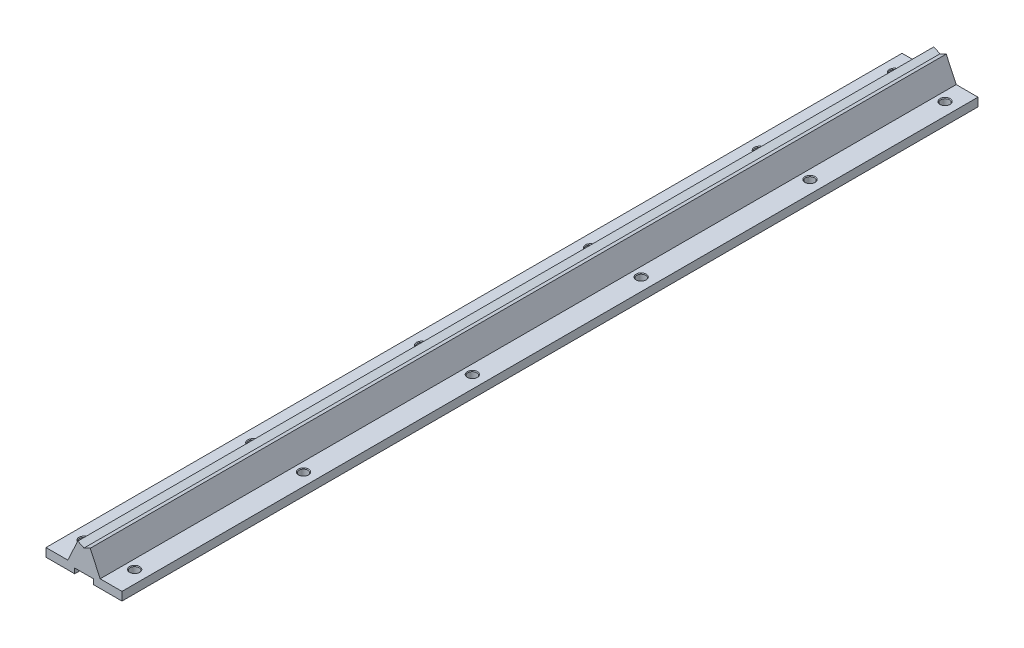
SolidWorks part; units mm, degrees
ref_plane "Front Plane" through (0, 0, 0) normal (0, 0, 1) x (1, 0, 0)
ref_plane "Top Plane" through (0, 0, 0) normal (0, 1, 0) x (1, 0, 0)
ref_plane "Right Plane" through (0, 0, 0) normal (1, 0, 0) x (0, 0, -1)
sketch "Sketch1" plane through (0, 0, 0) normal (0, 0, 1) x (1, 0, 0)
  line L0 (0, 0) -> (0, 30.5108) construction
  line L1 (0, 0) -> (-14.4586, 0) construction
  line L2 (5.5, 3) -> (-5.5, 3)
  line L3 (-5.5, 3) -> (-5.5, 0)
  line L4 (-5.5, 0) -> (-22.5, 0)
  line L5 (-22.5, 0) -> (-22.5, 5)
  line L6 (-22.5, 5) -> (-9.5977, 5)
  line L7 (-3.6756, 17.7) -> (3.6756, 17.7) construction
  line L8 (-3.6756, 17.7) -> (-9.5977, 5)
  line L9 (5.5, 3) -> (5.5, 0)
  line L10 (5.5, 0) -> (22.5, 0)
  line L11 (22.5, 0) -> (22.5, 5)
  line L12 (3.6756, 17.7) -> (9.5977, 5)
  line L13 (-3.6756, 17.7) -> (0, 15.986)
  line L14 (3.6756, 17.7) -> (0, 15.986)
  line L15 (9.5977, 5) -> (22.5, 5)
  circle A0 centre (0, 27) radius 10 construction
  point P16 (0, 3)
  point P19 (0, 5)
  dimension "D5" = 20
  dimension "D1" = 5.5
  dimension "D2" = 3
  dimension "D3" = 22.5
  dimension "D4" = 5
  dimension "D6" = 27
  dimension "D7" = 25
  dimension "D8" = 17.7
  dimension "D9" = 130
extrude "Boss-Extrude1" add sketch "Sketch1" along normal blind 507
sketch "Sketch2" plane through (0, 5, 0) normal (0, 1, 0) x (1, 0, 0)
  line L0 (0, 0) -> (0, -557.9877) construction
  line L1 (-15, -12) -> (-15, -550.3124) construction
  line L2 (-9.5977, 0) -> (-22.5, 0) construction
  circle A0 centre (-15, -12) radius 4
  circle A1 centre (-15, -92) radius 4
  circle A2 centre (-15, -192) radius 4
  circle A4 centre (-15, -292) radius 4.5615
  circle A5 centre (-15, -392) radius 4.5615
  circle A6 centre (-15, -492) radius 4.5615
  circle A7 centre (15, -492) radius 4.5615
  circle A8 centre (15, -392) radius 4.5615
  circle A9 centre (15, -292) radius 4.5615
  circle A10 centre (15, -192) radius 4
  circle A11 centre (15, -92) radius 4
  circle A12 centre (15, -12) radius 4
  dimension "D2" = 8
  dimension "D1" = 15
  dimension "D3" = 12
  dimension "D4" = 80
  dimension "D5" = 100
  dimension "D6" = 100
  dimension "D7" = 100
  dimension "D8" = 100
hole_wizard "Tap Drill for M5 Tap1" positions "3DSketch1" profile "Sketch3" hole size "M5" standard "GB"
sketch3d "3DSketch1"
  point P0 (-15, 5, 12)
  point P3 (15, 5, 12)
  point P6 (-15, 5, 92)
  point P9 (15, 5, 92)
  point P12 (-15, 5, 192)
  point P15 (15, 5, 192)
  point P18 (-15, 5, 292)
  point P21 (15, 5, 292)
  point P24 (-15, 5, 392)
  point P27 (15, 5, 392)
  point P30 (-15, 5, 492)
  point P33 (15, 5, 492)
sketch "Sketch3" plane through (-15, 5, 12) normal (1, 0, 0) x (0, 0, 1)
  line L0 (0, 0) -> (0, 47.5622)
  line L1 (0, 47.5622) -> (2.6, 46)
  line L2 (2.6, 46) -> (2.6, 0.4)
  line L3 (2.6, 0.4) -> (3, 0)
  line L5 (3, 0) -> (0, 0)
  line L6 (-2.6, 0.4) -> (-3, 0) construction
  line L10 (0, 47.5622) -> (-2.6, 46) construction
  line L11 (0, -6.35) -> (0, 107.95) construction
  dimension "Hole Dia." = 5.2
  dimension "Hole Depth" = 46
  dimension "Near C'Sink Dia." = 6
  dimension "Near C'Sink Angle" = 90
  dimension "Drill Angle" = 118
